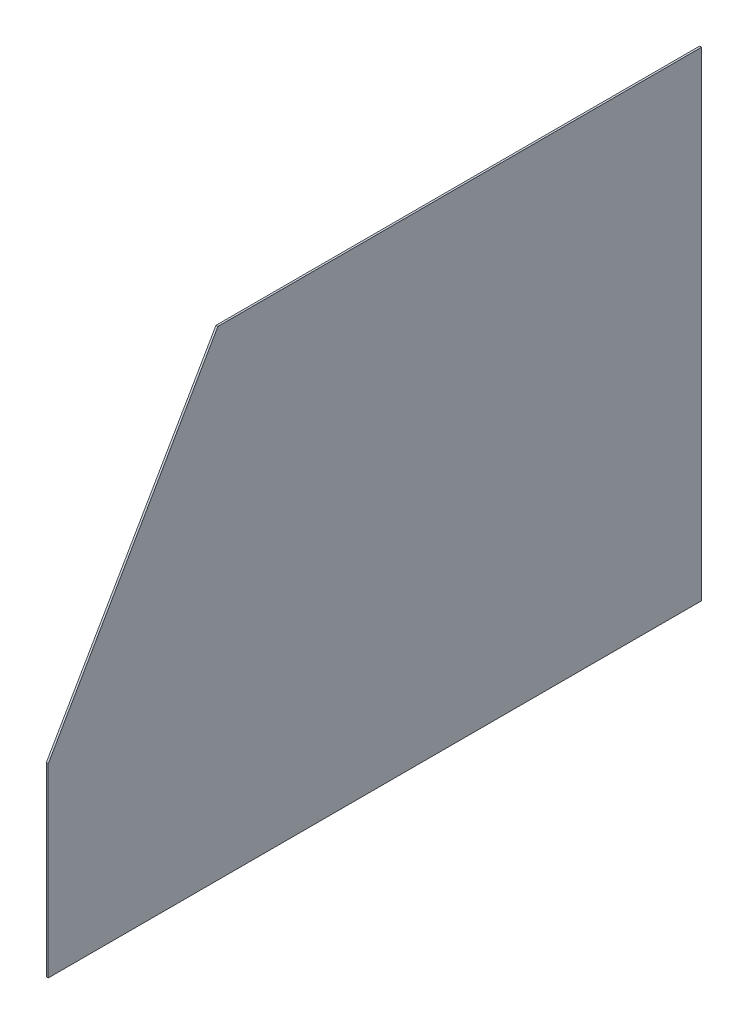
SolidWorks part; units mm, degrees
ref_plane "Front Plane" through (0, 0, 0) normal (0, 0, 1) x (1, 0, 0)
ref_plane "Top Plane" through (0, 0, 0) normal (0, 1, 0) x (1, 0, 0)
ref_plane "Right Plane" through (0, 0, 0) normal (1, 0, 0) x (0, 0, -1)
sketch "Sketch1" plane through (0, 0, 0) normal (1, 0, 0) x (0, 0, -1)
  line L0 (0, 0) -> (-794.5208, 0)
  line L1 (-794.5208, 0) -> (-1073.15, -482.6)
  line L2 (-1073.15, -482.6) -> (-1073.15, -787.4)
  line L3 (-1073.15, -787.4) -> (0, -787.4)
  line L4 (0, -787.4) -> (0, 0)
  dimension "D1" = 787.4
  dimension "D2" = 1073.15
  dimension "D3" = 30
  dimension "D4" = 304.8
  dimension "D5" = 794.5208
extrude "Boss-Extrude1" add sketch "Sketch1" along normal blind 3.175
sketch "Sketch2" plane through (3.175, 0, 0) normal (1, 0, 0) x (0, 0, -1)
  line L0 (-784.9575, 0) -> (-784.9575, -16.564) construction
  line L1 (0, 0) -> (-794.5208, 0) construction
  line L3 (-799.3024, -8.282) -> (-784.9575, -16.564) construction
  line L4 (-794.5208, 0) -> (-1073.15, -482.6) construction
  line L5 (-1073.15, -486.0105) -> (-1060.4217, -486.0105) construction
  line L6 (-1073.15, -482.6) -> (-1073.15, -787.4) construction
  line L7 (-1071.4447, -479.6464) -> (-1060.4217, -486.0105) construction
  line L8 (-1060.4217, -486.0105) -> (-1073.15, -482.6) construction
  line L9 (-784.9575, -16.564) -> (-794.5208, 0) construction
  dimension "D1" = 30
  dimension "D2" = 15
